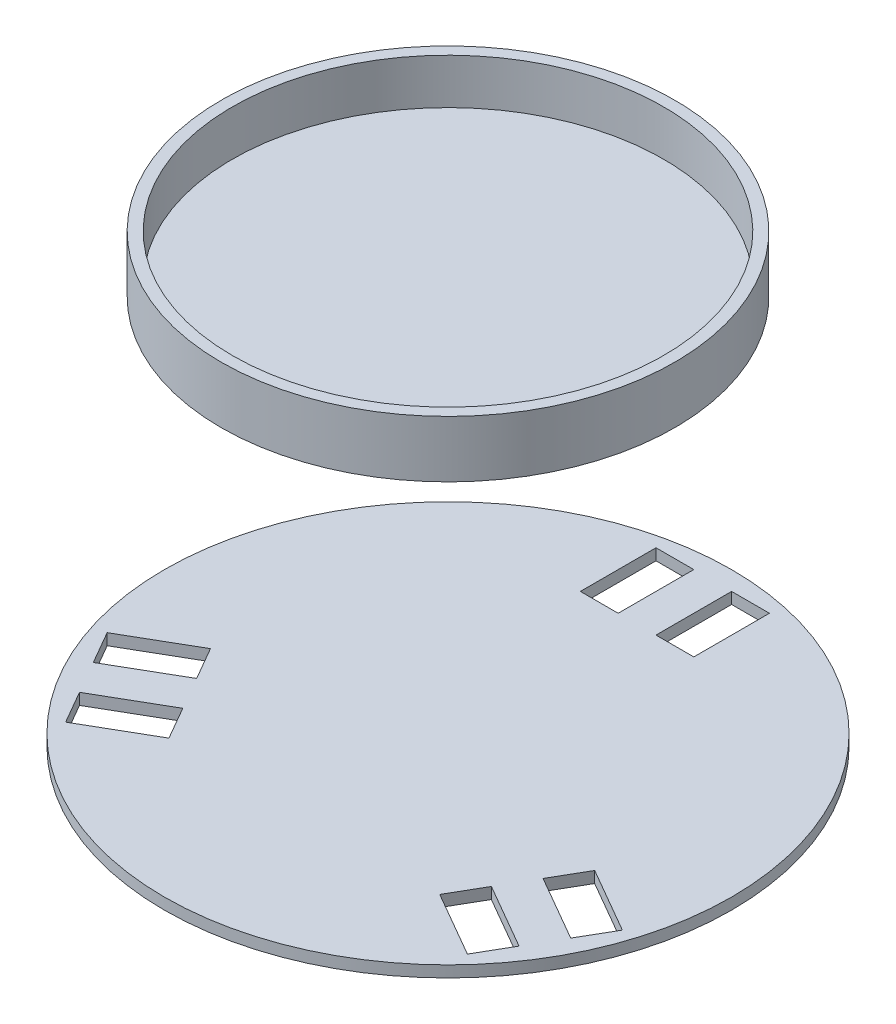
SolidWorks part; units mm, degrees
ref_plane "Front Plane" through (0, 0, 0) normal (0, 0, 1) x (1, 0, 0)
ref_plane "Top Plane" through (0, 0, 0) normal (0, 1, 0) x (1, 0, 0)
ref_plane "Right Plane" through (0, 0, 0) normal (1, 0, 0) x (0, 0, -1)
sketch "Sketch1" plane through (0, 0, 0) normal (0, 1, 0) x (1, 0, 0)
  circle A0 centre (0, 0) radius 150
  dimension "D1" = 300
extrude "Boss-Extrude1" add sketch "Sketch1" along normal blind 6
sketch "Sketch2" plane through (0, 6, 0) normal (0, 1, 0) x (1, 0, 0)
  line L0 (0, 0) -> (0, 150) construction
  line L1 (0, 0) -> (-150, 0) construction
  line L2 (-30, 140) -> (-30, 100)
  line L3 (10, 140) -> (30, 140)
  line L4 (10, 140) -> (10, 100)
  line L5 (10, 100) -> (30, 100)
  line L6 (30, 140) -> (30, 100)
  line L7 (-10, 100) -> (-30, 100)
  line L8 (-10, 140) -> (-10, 100)
  line L9 (-10, 140) -> (-30, 140)
  line L10 (126.2436, -61.3397) -> (91.6025, -41.3397)
  line L11 (126.2436, -61.3397) -> (136.2436, -44.0192)
  line L12 (136.2436, -44.0192) -> (101.6025, -24.0192)
  line L13 (91.6025, -41.3397) -> (101.6025, -24.0192)
  line L14 (116.2436, -78.6603) -> (81.6025, -58.6603)
  line L15 (116.2436, -78.6603) -> (106.2436, -95.9808)
  line L16 (106.2436, -95.9808) -> (71.6025, -75.9808)
  line L17 (81.6025, -58.6603) -> (71.6025, -75.9808)
  line L18 (-116.2436, -78.6603) -> (-81.6025, -58.6603)
  line L19 (-116.2436, -78.6603) -> (-106.2436, -95.9808)
  line L20 (-106.2436, -95.9808) -> (-71.6025, -75.9808)
  line L21 (-81.6025, -58.6603) -> (-71.6025, -75.9808)
  line L22 (-126.2436, -61.3397) -> (-91.6025, -41.3397)
  line L23 (-126.2436, -61.3397) -> (-136.2436, -44.0192)
  line L24 (-136.2436, -44.0192) -> (-101.6025, -24.0192)
  line L25 (-91.6025, -41.3397) -> (-101.6025, -24.0192)
  circle A0 centre (0, 0) radius 150 construction
  point P11 (20, 100)
  point P35 (0, 0)
  dimension "D1" = 40
  dimension "D2" = 20
  dimension "D3" = 10
  dimension "D4" = 100
  dimension "D5" = 3
extrude "Cut-Extrude1" cut sketch "Sketch2" against normal blind 6
ref_plane "Plane1" through (0, 206, 0) normal (0, 1, 0) x (1, 0, 0)
sketch "Sketch3" plane through (0, 206, 0) normal (0, 1, 0) x (1, 0, 0)
  circle A0 centre (0, 0) radius 120
  dimension "D1" = 240
extrude "Boss-Extrude2" add sketch "Sketch3" along normal blind 6 separate body
sketch "Sketch5" plane through (0, 212, 0) normal (0, 1, 0) x (1, 0, 0)
  circle A0 centre (0, 0) radius 114
  circle A2 centre (0, 0) radius 120
  dimension "D1" = 228
extrude "Boss-Extrude4" add sketch "Sketch5" along normal blind 24
